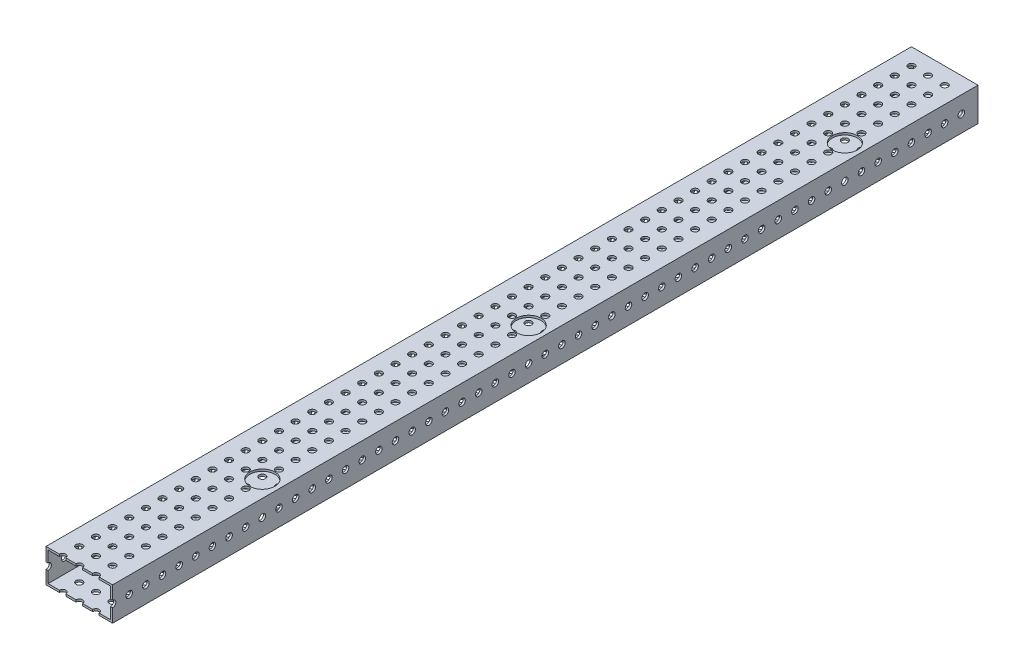
SolidWorks part; units mm, degrees
ref_plane "Front Plane" through (0, 0, 0) normal (0, 0, 1) x (1, 0, 0)
ref_plane "Top Plane" through (0, 0, 0) normal (0, 1, 0) x (1, 0, 0)
ref_plane "Right Plane" through (0, 0, 0) normal (1, 0, 0) x (0, 0, -1)
sketch "Sketch1" plane through (0, 0, 0) normal (0, 0, 1) x (1, 0, 0)
  line L0 (1.5875, 1.5875) -> (49.2125, 1.5875)
  line L1 (0, 0) -> (50.8, 0)
  line L2 (0, 0) -> (0, 25.4)
  line L3 (0, 25.4) -> (50.8, 25.4)
  line L4 (50.8, 0) -> (50.8, 25.4)
  line L5 (49.2125, 1.5875) -> (49.2125, 23.8125)
  line L6 (1.5875, 23.8125) -> (49.2125, 23.8125)
  line L7 (1.5875, 1.5875) -> (1.5875, 23.8125)
  dimension "D1" = 50.8
  dimension "D2" = 25.4
  dimension "D3" = 1.5875
extrude "Boss-Extrude1" add sketch "Sketch1" along normal blind 660.4
sketch "Sketch2" plane through (0, 25.4, 0) normal (0, 1, 0) x (1, 0, 0)
  line L0 (50.8, 0) -> (0, 0) construction
  line L1 (0, -660.4) -> (0, 0) construction
  line L2 (12.7, -12.7) -> (25.4, -12.7) construction
  line L3 (12.7, -12.7) -> (12.7, -25.4) construction
  circle A0 centre (12.7, -12.7) radius 2.4892
  circle A1 centre (25.4, -12.7) radius 2.4892
  circle A2 centre (38.1, -12.7) radius 2.4892
  circle A3 centre (25.4, -25.4) radius 2.4892
  circle A4 centre (38.1, -25.4) radius 2.4892
  circle A5 centre (25.4, -38.1) radius 2.4892
  circle A6 centre (38.1, -38.1) radius 2.4892
  circle A7 centre (25.4, -50.8) radius 2.4892
  circle A8 centre (38.1, -50.8) radius 2.4892
  circle A9 centre (25.4, -63.5) radius 2.4892
  circle A10 centre (38.1, -63.5) radius 2.4892
  circle A11 centre (25.4, -76.2) radius 2.4892
  circle A12 centre (38.1, -76.2) radius 2.4892
  circle A13 centre (25.4, -88.9) radius 2.4892
  circle A14 centre (38.1, -88.9) radius 2.4892
  circle A15 centre (25.4, -101.6) radius 2.4892
  circle A16 centre (38.1, -101.6) radius 2.4892
  circle A17 centre (25.4, -114.3) radius 2.4892
  circle A18 centre (38.1, -114.3) radius 2.4892
  circle A19 centre (25.4, -127) radius 2.4892
  circle A20 centre (38.1, -127) radius 2.4892
  circle A21 centre (25.4, -139.7) radius 2.4892
  circle A22 centre (38.1, -139.7) radius 2.4892
  circle A23 centre (25.4, -152.4) radius 2.4892
  circle A24 centre (38.1, -152.4) radius 2.4892
  circle A25 centre (25.4, -165.1) radius 2.4892
  circle A26 centre (38.1, -165.1) radius 2.4892
  circle A27 centre (25.4, -177.8) radius 2.4892
  circle A28 centre (38.1, -177.8) radius 2.4892
  circle A29 centre (25.4, -190.5) radius 2.4892
  circle A30 centre (38.1, -190.5) radius 2.4892
  circle A31 centre (25.4, -203.2) radius 2.4892
  circle A32 centre (38.1, -203.2) radius 2.4892
  circle A33 centre (25.4, -215.9) radius 2.4892
  circle A34 centre (38.1, -215.9) radius 2.4892
  circle A35 centre (25.4, -228.6) radius 2.4892
  circle A36 centre (38.1, -228.6) radius 2.4892
  circle A37 centre (25.4, -241.3) radius 2.4892
  circle A38 centre (38.1, -241.3) radius 2.4892
  circle A39 centre (25.4, -254) radius 2.4892
  circle A40 centre (38.1, -254) radius 2.4892
  circle A41 centre (25.4, -266.7) radius 2.4892
  circle A42 centre (38.1, -266.7) radius 2.4892
  circle A43 centre (25.4, -279.4) radius 2.4892
  circle A44 centre (38.1, -279.4) radius 2.4892
  circle A45 centre (25.4, -292.1) radius 2.4892
  circle A46 centre (38.1, -292.1) radius 2.4892
  circle A47 centre (25.4, -304.8) radius 2.4892
  circle A48 centre (38.1, -304.8) radius 2.4892
  circle A49 centre (25.4, -317.5) radius 2.4892
  circle A50 centre (38.1, -317.5) radius 2.4892
  circle A51 centre (25.4, -330.2) radius 2.4892
  circle A52 centre (38.1, -330.2) radius 2.4892
  circle A53 centre (25.4, -342.9) radius 2.4892
  circle A54 centre (38.1, -342.9) radius 2.4892
  circle A55 centre (25.4, -355.6) radius 2.4892
  circle A56 centre (38.1, -355.6) radius 2.4892
  circle A57 centre (25.4, -368.3) radius 2.4892
  circle A58 centre (38.1, -368.3) radius 2.4892
  circle A59 centre (25.4, -381) radius 2.4892
  circle A60 centre (38.1, -381) radius 2.4892
  circle A61 centre (25.4, -393.7) radius 2.4892
  circle A62 centre (38.1, -393.7) radius 2.4892
  circle A63 centre (25.4, -406.4) radius 2.4892
  circle A64 centre (38.1, -406.4) radius 2.4892
  circle A65 centre (25.4, -419.1) radius 2.4892
  circle A66 centre (38.1, -419.1) radius 2.4892
  circle A67 centre (25.4, -431.8) radius 2.4892
  circle A68 centre (38.1, -431.8) radius 2.4892
  circle A69 centre (25.4, -444.5) radius 2.4892
  circle A70 centre (38.1, -444.5) radius 2.4892
  circle A71 centre (25.4, -457.2) radius 2.4892
  circle A72 centre (38.1, -457.2) radius 2.4892
  circle A73 centre (25.4, -469.9) radius 2.4892
  circle A74 centre (38.1, -469.9) radius 2.4892
  circle A75 centre (25.4, -482.6) radius 2.4892
  circle A76 centre (38.1, -482.6) radius 2.4892
  circle A77 centre (25.4, -495.3) radius 2.4892
  circle A78 centre (38.1, -495.3) radius 2.4892
  circle A79 centre (25.4, -508) radius 2.4892
  circle A80 centre (38.1, -508) radius 2.4892
  circle A81 centre (25.4, -520.7) radius 2.4892
  circle A82 centre (38.1, -520.7) radius 2.4892
  circle A83 centre (25.4, -533.4) radius 2.4892
  circle A84 centre (38.1, -533.4) radius 2.4892
  circle A85 centre (25.4, -546.1) radius 2.4892
  circle A86 centre (38.1, -546.1) radius 2.4892
  circle A87 centre (25.4, -558.8) radius 2.4892
  circle A88 centre (38.1, -558.8) radius 2.4892
  circle A89 centre (25.4, -571.5) radius 2.4892
  circle A90 centre (38.1, -571.5) radius 2.4892
  circle A91 centre (25.4, -584.2) radius 2.4892
  circle A92 centre (38.1, -584.2) radius 2.4892
  circle A93 centre (25.4, -596.9) radius 2.4892
  circle A94 centre (38.1, -596.9) radius 2.4892
  circle A95 centre (25.4, -609.6) radius 2.4892
  circle A96 centre (38.1, -609.6) radius 2.4892
  circle A97 centre (25.4, -622.3) radius 2.4892
  circle A98 centre (38.1, -622.3) radius 2.4892
  circle A99 centre (25.4, -635) radius 2.4892
  circle A100 centre (38.1, -635) radius 2.4892
  circle A101 centre (25.4, -647.7) radius 2.4892
  circle A102 centre (38.1, -647.7) radius 2.4892
  circle A103 centre (25.4, -660.4) radius 2.4892
  circle A104 centre (38.1, -660.4) radius 2.4892
  circle A105 centre (12.7, -25.4) radius 2.4892
  circle A106 centre (12.7, -38.1) radius 2.4892
  circle A107 centre (12.7, -50.8) radius 2.4892
  circle A108 centre (12.7, -63.5) radius 2.4892
  circle A109 centre (12.7, -76.2) radius 2.4892
  circle A110 centre (12.7, -88.9) radius 2.4892
  circle A111 centre (12.7, -101.6) radius 2.4892
  circle A112 centre (12.7, -114.3) radius 2.4892
  circle A113 centre (12.7, -127) radius 2.4892
  circle A114 centre (12.7, -139.7) radius 2.4892
  circle A115 centre (12.7, -152.4) radius 2.4892
  circle A116 centre (12.7, -165.1) radius 2.4892
  circle A117 centre (12.7, -177.8) radius 2.4892
  circle A118 centre (12.7, -190.5) radius 2.4892
  circle A119 centre (12.7, -203.2) radius 2.4892
  circle A120 centre (12.7, -215.9) radius 2.4892
  circle A121 centre (12.7, -228.6) radius 2.4892
  circle A122 centre (12.7, -241.3) radius 2.4892
  circle A123 centre (12.7, -254) radius 2.4892
  circle A124 centre (12.7, -266.7) radius 2.4892
  circle A125 centre (12.7, -279.4) radius 2.4892
  circle A126 centre (12.7, -292.1) radius 2.4892
  circle A127 centre (12.7, -304.8) radius 2.4892
  circle A128 centre (12.7, -317.5) radius 2.4892
  circle A129 centre (12.7, -330.2) radius 2.4892
  circle A130 centre (12.7, -342.9) radius 2.4892
  circle A131 centre (12.7, -355.6) radius 2.4892
  circle A132 centre (12.7, -368.3) radius 2.4892
  circle A133 centre (12.7, -381) radius 2.4892
  circle A134 centre (12.7, -393.7) radius 2.4892
  circle A135 centre (12.7, -406.4) radius 2.4892
  circle A136 centre (12.7, -419.1) radius 2.4892
  circle A137 centre (12.7, -431.8) radius 2.4892
  circle A138 centre (12.7, -444.5) radius 2.4892
  circle A139 centre (12.7, -457.2) radius 2.4892
  circle A140 centre (12.7, -469.9) radius 2.4892
  circle A141 centre (12.7, -482.6) radius 2.4892
  circle A142 centre (12.7, -495.3) radius 2.4892
  circle A143 centre (12.7, -508) radius 2.4892
  circle A144 centre (12.7, -520.7) radius 2.4892
  circle A145 centre (12.7, -533.4) radius 2.4892
  circle A146 centre (12.7, -546.1) radius 2.4892
  circle A147 centre (12.7, -558.8) radius 2.4892
  circle A148 centre (12.7, -571.5) radius 2.4892
  circle A149 centre (12.7, -584.2) radius 2.4892
  circle A150 centre (12.7, -596.9) radius 2.4892
  circle A151 centre (12.7, -609.6) radius 2.4892
  circle A152 centre (12.7, -622.3) radius 2.4892
  circle A153 centre (12.7, -635) radius 2.4892
  circle A154 centre (12.7, -647.7) radius 2.4892
  circle A155 centre (12.7, -660.4) radius 2.4892
  dimension "D1" = 12.7
  dimension "D3" = 4.9784
  dimension "D2" = 12.7
  dimension "D6" = 90
  dimension "D7" = 12.7
  dimension "D8" = 12.7
  dimension "D4" = 3
  dimension "D5" = 52
extrude "Cut-Extrude1" cut sketch "Sketch2" against normal through all
sketch "Sketch3" plane through (0, 0, 0) normal (-1, 0, 0) x (0, 0, 1)
  line L0 (0, 25.4) -> (0, 0) construction
  line L1 (660.4, 25.4) -> (0, 25.4) construction
  line L2 (12.7, 12.7) -> (25.4, 12.7) construction
  circle A0 centre (12.7, 12.7) radius 2.4892
  circle A1 centre (25.4, 12.7) radius 2.4892
  circle A2 centre (38.1, 12.7) radius 2.4892
  circle A3 centre (50.8, 12.7) radius 2.4892
  circle A4 centre (63.5, 12.7) radius 2.4892
  circle A5 centre (76.2, 12.7) radius 2.4892
  circle A6 centre (88.9, 12.7) radius 2.4892
  circle A7 centre (101.6, 12.7) radius 2.4892
  circle A8 centre (114.3, 12.7) radius 2.4892
  circle A9 centre (127, 12.7) radius 2.4892
  circle A10 centre (139.7, 12.7) radius 2.4892
  circle A11 centre (152.4, 12.7) radius 2.4892
  circle A12 centre (165.1, 12.7) radius 2.4892
  circle A13 centre (177.8, 12.7) radius 2.4892
  circle A14 centre (190.5, 12.7) radius 2.4892
  circle A15 centre (203.2, 12.7) radius 2.4892
  circle A16 centre (215.9, 12.7) radius 2.4892
  circle A17 centre (228.6, 12.7) radius 2.4892
  circle A18 centre (241.3, 12.7) radius 2.4892
  circle A19 centre (254, 12.7) radius 2.4892
  circle A20 centre (266.7, 12.7) radius 2.4892
  circle A21 centre (279.4, 12.7) radius 2.4892
  circle A22 centre (292.1, 12.7) radius 2.4892
  circle A23 centre (304.8, 12.7) radius 2.4892
  circle A24 centre (317.5, 12.7) radius 2.4892
  circle A25 centre (330.2, 12.7) radius 2.4892
  circle A26 centre (342.9, 12.7) radius 2.4892
  circle A27 centre (355.6, 12.7) radius 2.4892
  circle A28 centre (368.3, 12.7) radius 2.4892
  circle A29 centre (381, 12.7) radius 2.4892
  circle A30 centre (393.7, 12.7) radius 2.4892
  circle A31 centre (406.4, 12.7) radius 2.4892
  circle A32 centre (419.1, 12.7) radius 2.4892
  circle A33 centre (431.8, 12.7) radius 2.4892
  circle A34 centre (444.5, 12.7) radius 2.4892
  circle A35 centre (457.2, 12.7) radius 2.4892
  circle A36 centre (469.9, 12.7) radius 2.4892
  circle A37 centre (482.6, 12.7) radius 2.4892
  circle A38 centre (495.3, 12.7) radius 2.4892
  circle A39 centre (508, 12.7) radius 2.4892
  circle A40 centre (520.7, 12.7) radius 2.4892
  circle A41 centre (533.4, 12.7) radius 2.4892
  circle A42 centre (546.1, 12.7) radius 2.4892
  circle A43 centre (558.8, 12.7) radius 2.4892
  circle A44 centre (571.5, 12.7) radius 2.4892
  circle A45 centre (584.2, 12.7) radius 2.4892
  circle A46 centre (596.9, 12.7) radius 2.4892
  circle A47 centre (609.6, 12.7) radius 2.4892
  circle A48 centre (622.3, 12.7) radius 2.4892
  circle A49 centre (635, 12.7) radius 2.4892
  circle A50 centre (647.7, 12.7) radius 2.4892
  circle A51 centre (660.4, 12.7) radius 2.4892
  dimension "D1" = 12.7
  dimension "D3" = 4.9784
  dimension "D2" = 12.7
  dimension "D5" = 12.7
  dimension "D4" = 52
extrude "Cut-Extrude2" cut sketch "Sketch3" against normal through all
sketch "Sketch4" plane through (0, 0, 0) normal (0, -1, 0) x (1, 0, 0)
  circle A0 centre (38.1, 330.2) radius 9.525
  circle A1 centre (38.1, 88.9) radius 9.525
  circle A2 centre (38.1, 533.4) radius 9.525
  dimension "D1" = 19.05
extrude "Cut-Extrude3" cut sketch "Sketch4" against normal through all
